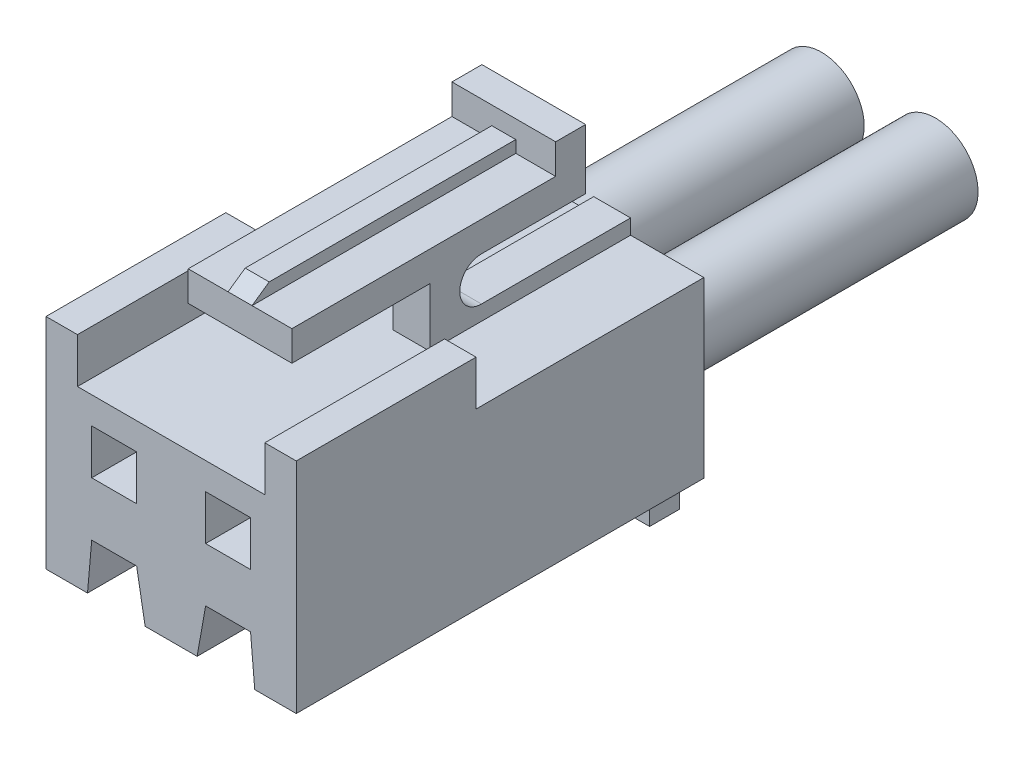
SolidWorks part; units mm, degrees
ref_plane "Plan de face" through (0, 0, 0) normal (0, 0, 1) x (1, 0, 0)
ref_plane "Plan de dessus" through (0, 0, 0) normal (0, 1, 0) x (1, 0, 0)
ref_plane "Plan de droite" through (0, 0, 0) normal (1, 0, 0) x (0, 0, -1)
sketch "Esquisse1" plane through (0, 0, 0) normal (0, 0, 1) x (1, 0, 0)
  line L0 (0, 0) -> (0, 1.65) construction
  line L1 (-4.175, 3.15) -> (-3.125, 3.15)
  line L2 (-4.175, 3.15) -> (-4.175, -4.15)
  line L3 (-4.175, -4.15) -> (4.175, -4.15)
  line L4 (4.175, 3.15) -> (4.175, -4.15)
  line L5 (-3.125, 3.15) -> (-3.125, 1.65)
  line L6 (-3.125, 1.65) -> (3.125, 1.65)
  line L7 (3.125, 1.65) -> (3.125, 3.15)
  line L8 (3.125, 3.15) -> (4.175, 3.15)
  line L9 (-1.15, 0) -> (0, 0) construction
  line L10 (-2.65, 0.75) -> (-1.15, 0.75)
  line L11 (-2.65, 0.75) -> (-2.65, -0.75)
  line L12 (-2.65, -0.75) -> (-1.15, -0.75)
  line L13 (-1.15, 0.75) -> (-1.15, -0.75)
  line L14 (1.15, 0.75) -> (1.15, -0.75)
  line L15 (2.65, -0.75) -> (1.15, -0.75)
  line L16 (2.65, 0.75) -> (2.65, -0.75)
  line L17 (2.65, 0.75) -> (1.15, 0.75)
  point P15 (-1.9, -0.75)
  dimension "D1" = 8.35
  dimension "D2" = 7.3
  dimension "D3" = 1.05
  dimension "D4" = 5.8
  dimension "D5" = 0.9
  dimension "D6" = 3.8
  dimension "D7" = 1.5
  dimension "D8" = 1.5
extrude "Boss.-Extru.1" add sketch "Esquisse1" against normal blind 13.6
sketch "Esquisse2" plane through (0, 0, 0) normal (1, 0, 0) x (0, 0, -1)
  line L0 (13.6, 1.65) -> (13.6, 3.15) construction
  line L1 (2.3, 4.6) -> (11.1, 4.6)
  line L2 (2.3, 4.6) -> (2.3, 3.6)
  line L3 (2.3, 3.6) -> (6.9, 3.6)
  line L4 (12.1, 5.6) -> (12.1, 3.6)
  line L5 (13.6, -4.15) -> (0, -4.15) construction
  line L6 (0, 4.5925) -> (0, -4.5925) construction
  line L7 (11.1, 4.6) -> (11.1, 5.6)
  line L8 (11.1, 5.6) -> (12.1, 5.6)
  line L9 (6.9, 3.6) -> (6.9, 1.65)
  line L10 (6.9, 1.65) -> (13.6, 1.65)
  line L11 (13.6, 1.65) -> (13.6, 2.15)
  line L12 (13.6, 2.15) -> (8.625, 2.15)
  line L13 (13.6, 1.65) -> (0, 1.65) construction
  line L14 (8.625, 3.6) -> (12.1, 3.6)
  arc A0 (8.625, 3.6) -> (8.625, 2.15) centre (8.625, 2.875) ccw
  point P8 (4.4, 3.6)
  dimension "D9" = 6.7
  dimension "D10" = 1
  dimension "D1" = 9.8
  dimension "D2" = 1.5
  dimension "D3" = 8.75
  dimension "D4" = 1
  dimension "D5" = 4.4
  dimension "D6" = 2
  dimension "D7" = 1
  dimension "D8" = 0.5
extrude "Boss.-Extru.2" add sketch "Esquisse2" along normal mid plane 3.46
sketch "Esquisse3" plane through (0, 0, 0) normal (1, 0, 0) x (0, 0, -1)
  line L0 (2.3, 4.6) -> (2.8713, 5)
  line L1 (2.8713, 5) -> (11.1, 5)
  line L2 (11.1, 5) -> (11.1, 4.6)
  line L3 (2.3, 4.6) -> (11.1, 4.6)
  line L5 (11.1, 5.6) -> (11.1, 4.6) construction
  line L6 (11.1, 4.6) -> (2.3, 4.6) construction
  dimension "D1" = 0.4
  dimension "D2" = 35
extrude "Boss.-Extru.3" add sketch "Esquisse3" along normal mid plane 0.8
sketch "Esquisse4" plane through (0, 0, 0) normal (1, 0, 0) x (0, 0, -1)
  line L0 (4.3, 3.6) -> (4.3, 2.8)
  line L1 (2.3, 3.6) -> (4.3, 2.8)
  line L2 (2.3, 3.6) -> (4.3, 3.6)
  dimension "D1" = 0.1
  dimension "D2" = 0.8
extrude "Boss.-Extru.4" add sketch "Esquisse4" along normal mid plane 0.8
sketch "Esquisse5" plane through (0, 0, -13.6) normal (0, 0, -1) x (-1, 0, 0)
  line L0 (0, 0) -> (0, 1.65) construction
  line L1 (-0.5, 3.6) -> (0.5, 3.6)
  line L2 (-0.5, 3.6) -> (-0.5, 1.65)
  line L3 (-0.5, 1.65) -> (0.5, 1.65)
  line L4 (0.5, 3.6) -> (0.5, 1.65)
  line L5 (-3.125, 1.65) -> (-1.73, 1.65) construction
  line L6 (-1.73, 3.6) -> (1.73, 3.6) construction
  dimension "D1" = 1
extrude "Enlèv. mat.-Extru.1" cut sketch "Esquisse5" against normal up to surface (6.7 mm away) up to face at (0, 2.625, -6.9)
sketch "Esquisse6" plane through (0, -4.15, 0) normal (0, -1, 0) x (1, 0, 0)
  line L0 (-4.175, -13.6) -> (4.175, -13.6) construction
  line L1 (3.365, -13.6) -> (-3.365, -13.6)
  line L2 (3.365, -13.6) -> (3.365, -12.6)
  line L3 (3.365, -12.6) -> (-3.365, -12.6)
  line L4 (-3.365, -13.6) -> (-3.365, -12.6)
  line L5 (0, 0) -> (0, -12.6) construction
  line L6 (-4.175, 0) -> (4.175, 0) construction
  dimension "D1" = 6.73
  dimension "D2" = 1
extrude "Boss.-Extru.5" add sketch "Esquisse6" along normal blind 1.3
sketch "Esquisse8" plane through (4.175, 0, 0) normal (1, 0, 0) x (0, 0, -1)
  line L0 (0, -4.15) -> (0, 3.15) construction
  line L1 (13.6, 3.15) -> (6, 3.15)
  line L2 (13.6, 3.15) -> (13.6, 1.65)
  line L3 (13.6, 1.65) -> (6, 1.65)
  line L4 (6, 3.15) -> (6, 1.65)
  line L5 (13.6, 1.65) -> (0, 1.65) construction
  dimension "D1" = 6
extrude "Enlèv. mat.-Extru.3" cut sketch "Esquisse8" against normal blind 1.1
mirror "Symétrie1" about plane through (0, 0, 0) normal (1, 0, 0) of "Enlèv. mat.-Extru.3"
sketch "Esquisse7" plane through (0, 0, -13.6) normal (0, 0, -1) x (-1, 0, 0)
  line L0 (-4.175, 1.65) -> (-1.73, 1.65) construction
  line L1 (-3.675, 1.15) -> (-0.25, 1.15)
  line L2 (-3.675, 1.15) -> (-3.675, -3.15)
  line L3 (-2.7, -3.65) -> (-1.1, -3.65)
  line L4 (-0.25, 1.15) -> (-0.25, -3.15)
  line L5 (-4.175, -4.15) -> (-4.175, 1.65) construction
  line L6 (-3.365, -4.15) -> (-4.175, -4.15) construction
  line L7 (0, 0) -> (0, -2.1419) construction
  line L8 (-3.675, -3.15) -> (-2.7, -3.15)
  line L9 (-2.7, -3.15) -> (-2.7, -3.65)
  line L10 (-1.1, -3.15) -> (-1.1, -3.65)
  line L11 (-1.1, -3.15) -> (-0.25, -3.15)
  line L12 (-1.9, -0.75) -> (-1.9, -3.65) construction
  line L13 (-1.15, -0.75) -> (-2.65, -0.75) construction
  line L14 (3.675, 1.15) -> (3.675, -3.15)
  line L15 (3.675, -3.15) -> (2.7, -3.15)
  line L16 (2.7, -3.15) -> (2.7, -3.65)
  line L17 (2.7, -3.65) -> (1.1, -3.65)
  line L18 (1.1, -3.15) -> (1.1, -3.65)
  line L19 (1.1, -3.15) -> (0.25, -3.15)
  line L20 (0.25, 1.15) -> (0.25, -3.15)
  line L21 (3.675, 1.15) -> (0.25, 1.15)
  dimension "D1" = 0.5
  dimension "D2" = 0.5
  dimension "D3" = 0.5
  dimension "D4" = 0.5
  dimension "D5" = 0.5
  dimension "D6" = 1.6
extrude "Enlèv. mat.-Extru.2" cut sketch "Esquisse7" against normal blind 11.6
sketch "Esquisse10" plane through (0, 0, 0) normal (0, 0, 1) x (1, 0, 0)
  line L0 (2.79, -4.15) -> (2.65, -2.55)
  line L1 (2.65, -2.55) -> (1.15, -2.55)
  line L2 (1.15, -2.55) -> (0.8679, -4.15)
  line L3 (0.8679, -4.15) -> (2.79, -4.15)
  line L4 (-4.175, -4.15) -> (4.175, -4.15) construction
  line L5 (2.65, -0.75) -> (2.65, 0.75) construction
  line L6 (1.15, 0.75) -> (1.15, -0.75) construction
  line L7 (4.175, -4.15) -> (4.175, 3.15) construction
  line L8 (0, 0) -> (0, -1.4887) construction
  line L9 (-0.8679, -4.15) -> (-2.79, -4.15)
  line L10 (-1.15, -2.55) -> (-0.8679, -4.15)
  line L11 (-2.65, -2.55) -> (-1.15, -2.55)
  line L12 (-2.79, -4.15) -> (-2.65, -2.55)
  dimension "D1" = 1.6
  dimension "D2" = 5
  dimension "D3" = 10
extrude "Enlèv. mat.-Extru.4" cut sketch "Esquisse10" against normal blind 5.8
sketch "Esquisse11" plane through (0, 0, -13.6) normal (0, 0, -1) x (-1, 0, 0)
  line L0 (-1.9, 0.75) -> (-1.9, -1.3) construction
  line L1 (-2.65, 0.75) -> (-1.15, 0.75) construction
  line L2 (4.5925, 0) -> (-4.5925, 0) construction
  line L3 (0, 0) -> (0, -0.7678) construction
  circle A0 centre (-1.9, -1.3) radius 1.425
  circle A1 centre (1.9, -1.3) radius 1.425
  dimension "D1" = 2.85
  dimension "D2" = 1.3
extrude "Boss.-Extru.6" add sketch "Esquisse11" along normal blind 10 and the other way blind 3 separate body
